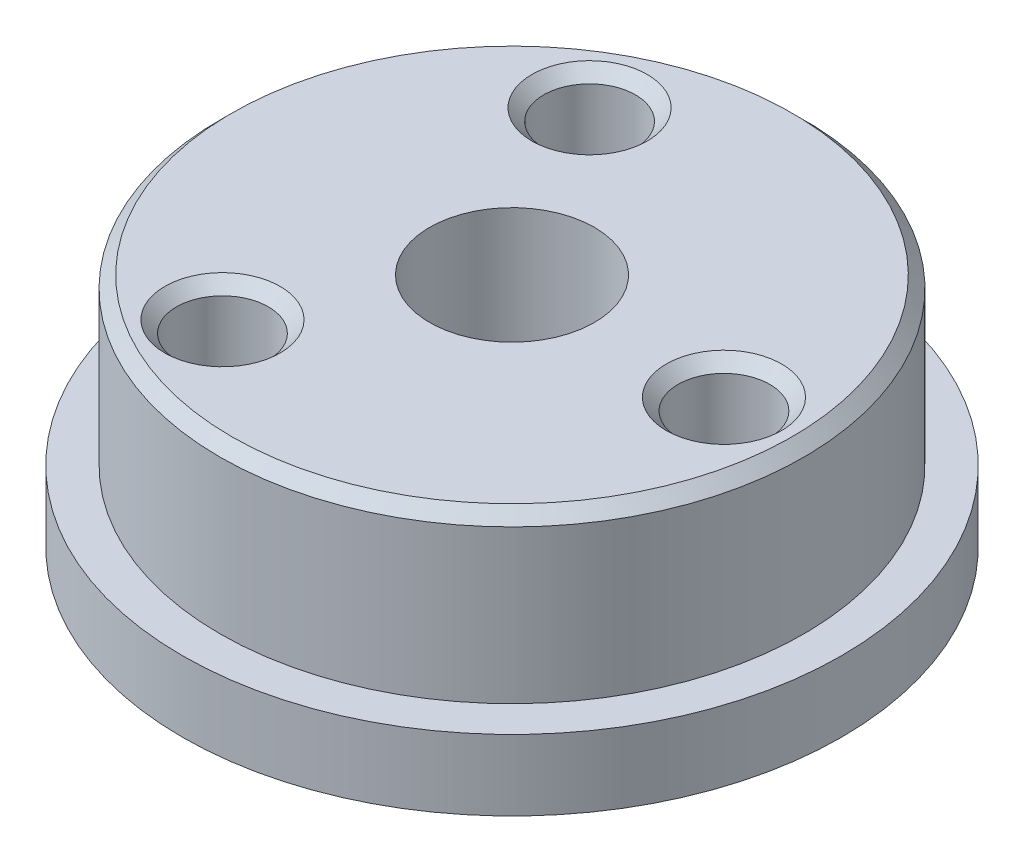
SolidWorks part; units mm, degrees
ref_plane "前视基准面" through (0, 0, 0) normal (0, 0, 1) x (1, 0, 0)
ref_plane "上视基准面" through (0, 0, 0) normal (0, 1, 0) x (1, 0, 0)
ref_plane "右视基准面" through (0, 0, 0) normal (1, 0, 0) x (0, 0, -1)
other "Configuration Table"
sketch "草图1" plane through (0, 0, 0) normal (0, 1, 0) x (1, 0, 0)
  circle A0 centre (0, 0) radius 14
  dimension "D1" = 28
extrude "凸台-拉伸1" add sketch "草图1" along normal blind 3
sketch "草图2" plane through (0, 3, 0) normal (0, 1, 0) x (1, 0, 0)
  circle A0 centre (0, 0) radius 12.4
  dimension "D1" = 24.8
extrude "凸台-拉伸2" add sketch "草图2" along normal blind 7
sketch "草图3" plane through (0, 0, 0) normal (0, -1, 0) x (1, 0, 0)
  circle A0 centre (10.5, 0) radius 1.65
  circle A1 centre (5.25, -9.0933) radius 1.65
  circle A2 centre (-5.25, -9.0933) radius 1.65
  circle A3 centre (-10.5, 0) radius 1.65
  circle A4 centre (-5.25, 9.0933) radius 1.65
  circle A5 centre (5.25, 9.0933) radius 1.65
  point P16 (0, 0)
  dimension "D1" = 10.5
  dimension "D2" = 3.3
  dimension "D3" = 6
extrude "切除-拉伸1" cut sketch "草图3" against normal blind 5.1
sketch "草图4" plane through (0, 0, 0) normal (0, -1, 0) x (1, 0, 0)
  circle A0 centre (0, 0) radius 3.5
  dimension "D1" = 7
extrude "切除-拉伸2" cut sketch "草图4" against normal through all
sketch "草图6" plane through (0, 10, 0) normal (0, 1, 0) x (1, 0, 0)
  circle A0 centre (9, 0) radius 1.95
  circle A1 centre (-4.5, -7.7942) radius 1.95
  circle A2 centre (-4.5, 7.7942) radius 1.95
  point P10 (0, 0)
  dimension "D1" = 3.9
  dimension "D2" = 9
  dimension "D3" = 3
extrude "切除-拉伸4" cut sketch "草图6" against normal blind 3.2
chamfer "倒角1" distance 0.5 angle 45 4 edges at (-4.5, 10, 9.7442) (9, 10, 1.95) (-4.5, 10, -5.8442) (0, 10, 12.4)
